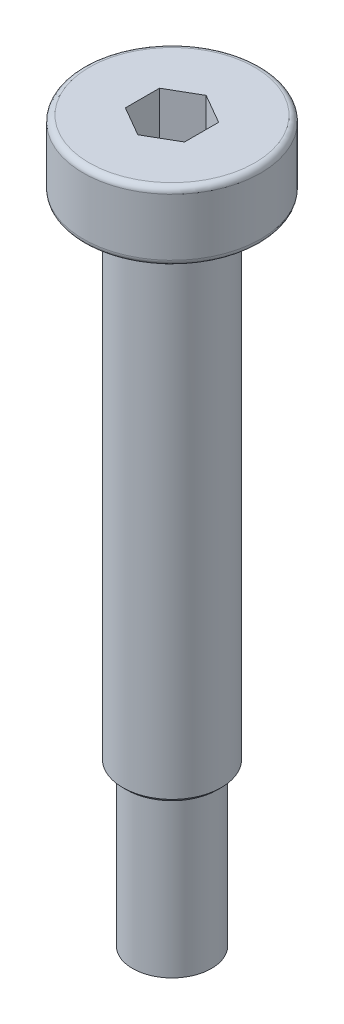
SolidWorks part; units mm, degrees
ref_plane "Front Plane" through (0, 0, 0) normal (0, 0, 1) x (1, 0, 0)
ref_plane "Top Plane" through (0, 0, 0) normal (0, 1, 0) x (1, 0, 0)
ref_plane "Right Plane" through (0, 0, 0) normal (1, 0, 0) x (0, 0, -1)
sketch "Sketch1" plane through (0, 0, 0) normal (0, 0, 1) x (1, 0, 0)
  line L0 (0, 0) -> (0, -29.1917) construction
  line L1 (0, 3.5) -> (-4.5, 3.5)
  line L2 (-4.5, 3.5) -> (-4.5, 0)
  line L3 (-4.5, 0) -> (-2.5, 0)
  line L4 (-2.5, 0) -> (-2.5, -25)
  line L5 (-2.5, -25) -> (-2, -25)
  line L6 (-2, -25) -> (-2, -33)
  line L7 (-2, -33) -> (0, -33)
  line L8 (0, 0) -> (0, 8.6899) construction
  line L9 (0, 3.5) -> (0, -33)
  dimension "D1" = 5
  dimension "D2" = 4
  dimension "D3" = 8
  dimension "D4" = 9
  dimension "D5" = 3.5
  dimension "D6" = 25
revolve "Revolve1" add sketch "Sketch1" angle 360 about L9
cosmetic thread "Cosmetic Thread1" parameters "D2"=3.242
fillet "Fillet1" radius 0.3 2 edges at (-4.5, 0, 0) (-4.5, 3.5, 0)
sketch "Sketch2" plane through (0, 3.5, 0) normal (0, 1, 0) x (1, 0, 0)
  line L1 (1.5, 0.866) -> (0, 1.7321)
  line L2 (0, 1.7321) -> (-1.5, 0.866)
  line L3 (-1.5, 0.866) -> (-1.5, -0.866)
  line L4 (-1.5, -0.866) -> (0, -1.7321)
  line L5 (0, -1.7321) -> (1.5, -0.866)
  line L6 (1.5, -0.866) -> (1.5, 0.866)
  circle A0 centre (0, 0) radius 1.5 construction
  dimension "D1" = 3
extrude "Cut-Extrude1" cut sketch "Sketch2" against normal blind 2.4
chamfer "Chamfer1" distance 0.2 angle 45 1 edges at (-2.5, -25, 0)
